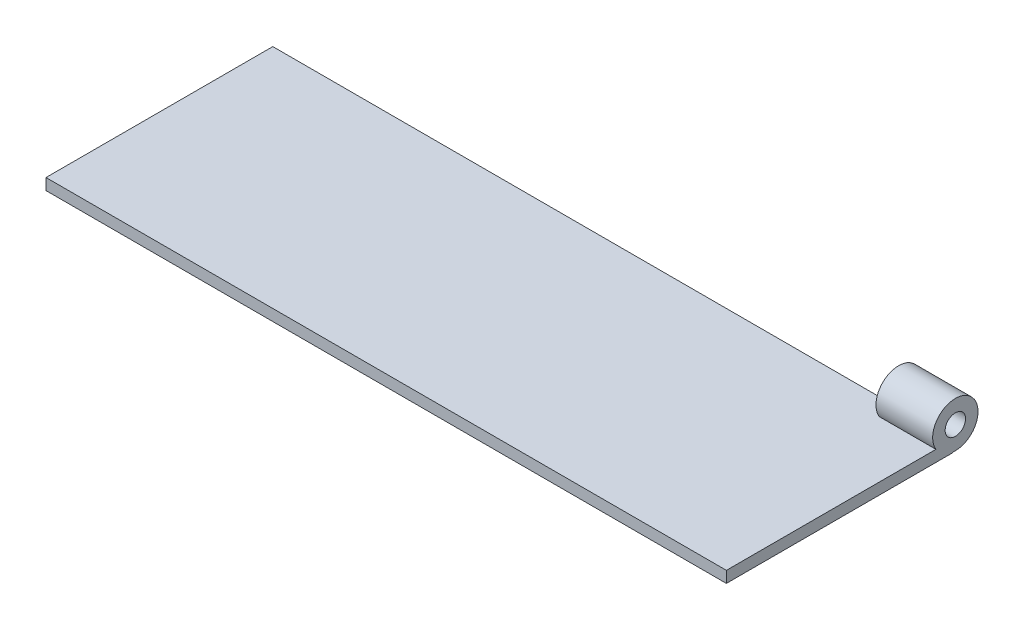
SolidWorks part; units mm, degrees
ref_plane "Front Plane" through (0, 0, 0) normal (0, 0, 1) x (1, 0, 0)
ref_plane "Top Plane" through (0, 0, 0) normal (0, 1, 0) x (1, 0, 0)
ref_plane "Right Plane" through (0, 0, 0) normal (1, 0, 0) x (0, 0, -1)
sketch "Sketch1" plane through (0, 0, 0) normal (0, 1, 0) x (1, 0, 0)
  line L1 (150, 50) -> (-150, 50)
  line L2 (150, 50) -> (150, -50)
  line L3 (150, -50) -> (-150, -50)
  line L4 (-150, 50) -> (-150, -50)
  line L5 (150, 50) -> (-150, -50) construction
  line L6 (150, -50) -> (-150, 50) construction
  point P0 (0, 0)
  dimension "D1" = 300
  dimension "D2" = 100
extrude "Boss-Extrude1" add sketch "Sketch1" along normal blind 5
ref_plane "Plane1" through (150, 0, 0) normal (1, 0, 0) x (0, 0, -1)
sketch "Sketch7" plane through (150, 0, 0) normal (1, 0, 0) x (0, 0, -1)
  circle A0 centre (50.9542, 10.1723) radius 10
extrude "Boss-Extrude5" add sketch "Sketch7" against normal blind 25 contours A0
sketch "Sketch10" plane through (150, 0, 0) normal (1, 0, 0) x (0, 0, -1)
  circle A0 centre (50.9542, 10.1723) radius 4.5
  point P3 (0, 0)
sketch "Sketch12" plane through (150, 0, 0) normal (1, 0, 0) x (0, 0, -1)
extrude "Cut-Extrude1" cut sketch "Sketch10" against normal blind 25
